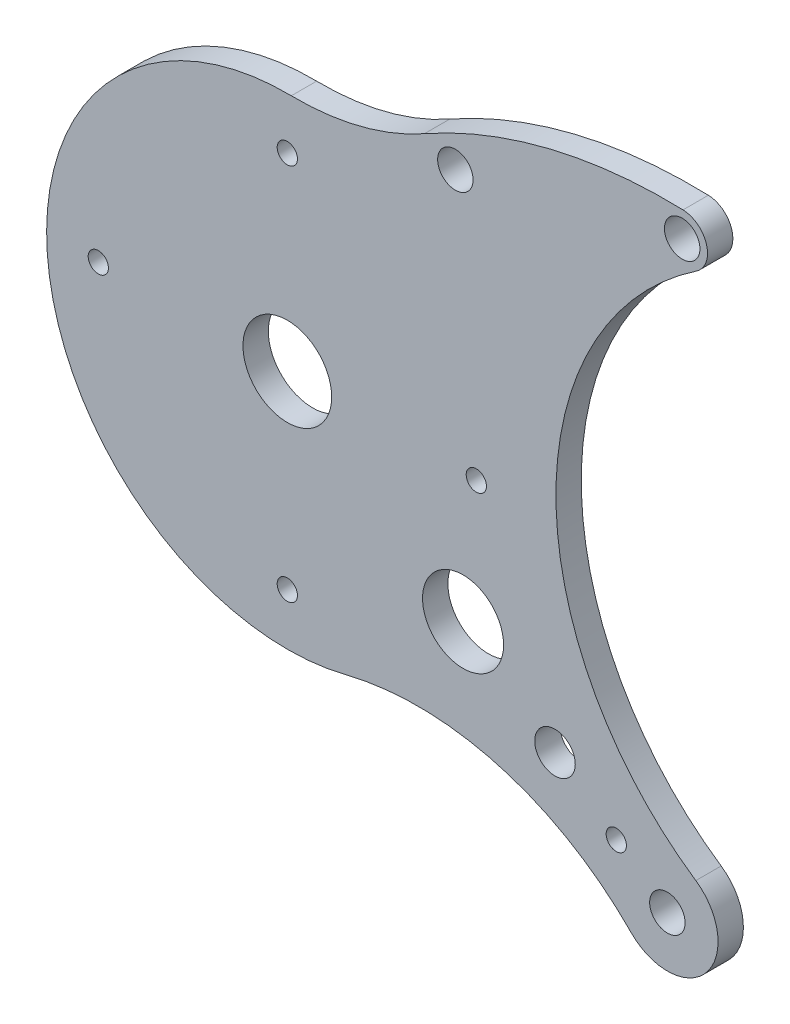
SolidWorks part; units mm, degrees
ref_plane "Front Plane" through (0, 0, 0) normal (0, 0, 1) x (1, 0, 0)
ref_plane "Top Plane" through (0, 0, 0) normal (0, 1, 0) x (1, 0, 0)
ref_plane "Right Plane" through (0, 0, 0) normal (1, 0, 0) x (0, 0, -1)
sketch "Sketch1" plane through (0, 0, 0) normal (0, 0, 1) x (1, 0, 0)
  arc A0 (1.5722, 94.987) -> (23.0489, -92.1615) centre (0, 0) ccw
  arc A1 (135.7114, -123.9942) -> (161.2252, -93.4472) centre (150, -110) ccw
  arc A2 (54.1221, 108.2997) -> (156.1718, 133.2815) centre (149.8103, -61.6578) cw
  arc A3 (161.4411, 114.9988) -> (156.1718, 133.2815) centre (155.8457, 123.2868) ccw
  arc A4 (54.1221, 108.2997) -> (1.5722, 94.987) centre (3.287, 198.5908) cw
  arc A5 (23.0489, -92.1615) -> (135.7114, -123.9942) centre (51.6099, -206.3628) cw
  arc A6 (161.2252, -93.4472) -> (161.4411, 114.9988) centre (231.8536, 10.7027) cw
  circle A7 centre (66.321, 102.0892) radius 7
  circle A8 centre (155.8457, 123.2868) radius 7
  circle A9 centre (150, -110) radius 7
  circle A10 centre (0, 74.6) radius 4
  circle A11 centre (74.6, 0) radius 4
  circle A12 centre (0, -74.6) radius 4
  circle A13 centre (-74.6, 0) radius 4
  circle A14 centre (0, 0) radius 17.5
  point P3 (66.321, 102.0892)
  point P4 (150, -110)
  point P5 (155.8457, 123.2868)
  point P35 (0, 0)
  point P36 (0, 0)
  point P37 (0, 0)
  dimension "D7" = 95
  dimension "D8" = 10
  dimension "D9" = 20
  dimension "D10" = 8
  dimension "D11" = 14
  dimension "D12" = 14
  dimension "D13" = 14
  dimension "D14" = 35
  dimension "D2" = 228
  dimension "D3" = 150
  dimension "D4" = 110
  dimension "D5" = 92
  dimension "D6" = 233.36
extrude "Boss-Extrude1" add sketch "Sketch1" along normal blind 10
sketch "Sketch4" plane through (0, 0, 10) normal (0, 0, 1) x (1, 0, 0)
  line L0 (0, 0) -> (150, -110) construction
  circle A0 centre (129.8399, -95.2159) radius 4
  circle A1 centre (105.6477, -77.475) radius 8
  circle A2 centre (69.3595, -50.8636) radius 16
  dimension "D4" = 8
  dimension "D5" = 16
  dimension "D6" = 32
  dimension "D1" = 30
  dimension "D2" = 45
  dimension "D3" = 25
extrude "Cut-Extrude1" cut sketch "Sketch4" against normal through all
